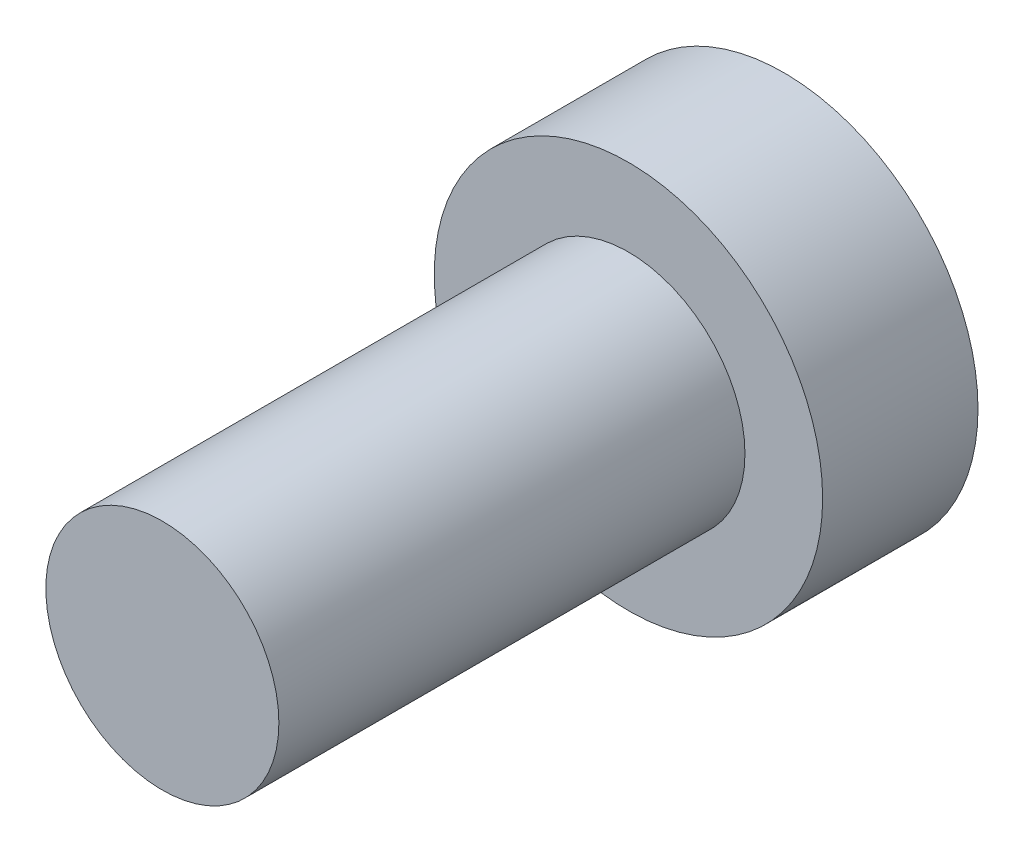
SolidWorks part; units mm, degrees
ref_plane "Front Plane" through (0, 0, 0) normal (0, 0, 1) x (1, 0, 0)
ref_plane "Top Plane" through (0, 0, 0) normal (0, 1, 0) x (1, 0, 0)
ref_plane "Right Plane" through (0, 0, 0) normal (1, 0, 0) x (0, 0, -1)
sketch "Sketch1" plane through (0, 0, 0) normal (0, 0, 1) x (1, 0, 0)
  circle A0 centre (0, 0) radius 2.5
extrude "Boss-Extrude1" add sketch "Sketch1" along normal blind 2
sketch "Sketch2" plane through (0, 0, 2) normal (0, 0, 1) x (1, 0, 0)
  circle A0 centre (0, 0) radius 1.5
extrude "Boss-Extrude2" add sketch "Sketch2" along normal blind 6
